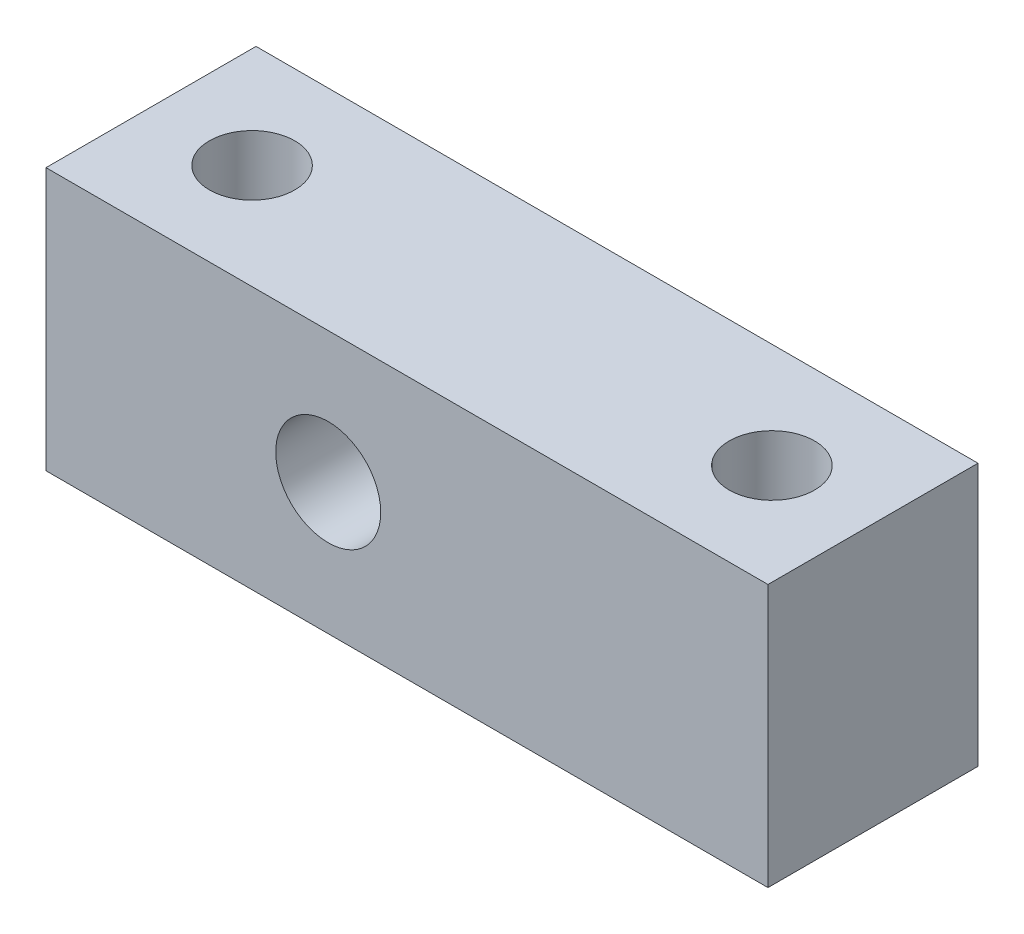
SolidWorks part; units mm, degrees
ref_plane "Спереди" through (0, 0, 0) normal (0, 0, 1) x (1, 0, 0)
ref_plane "Сверху" through (0, 0, 0) normal (0, 1, 0) x (1, 0, 0)
ref_plane "Справа" through (0, 0, 0) normal (1, 0, 0) x (0, 0, -1)
sketch "Эскиз1" plane through (0, 0, 0) normal (0, 0, 1) x (1, 0, 0)
  line L1 (-27.5, -10) -> (27.5, -10)
  line L2 (-27.5, -10) -> (-27.5, 10)
  line L3 (-27.5, 10) -> (27.5, 10)
  line L4 (27.5, -10) -> (27.5, 10)
  line L5 (-27.5, -10) -> (27.5, 10) construction
  line L6 (-27.5, 10) -> (27.5, -10) construction
  point P0 (0, 0)
  dimension "D1" = 55
  dimension "D2" = 20
extrude "Бобышка-Вытянуть1" add sketch "Эскиз1" along normal blind 16
sketch "Эскиз2" plane through (0, 0, 16) normal (0, 0, 1) x (1, 0, 0)
  circle A0 centre (-6, 0) radius 4
  dimension "D1" = 8
  dimension "D2" = 6
extrude "Вырез-Вытянуть1" cut sketch "Эскиз2" against normal blind 18
hole_wizard "Диаметр отверстия Ø6.5 (6.5)1" positions "Эскиз3" profile "Эскиз4" hole size "Ø6.5" standard "DIN" end condition through all
sketch "Эскиз3" plane through (0, 10, 0) normal (0, 1, 0) x (1, 0, 0)
  line L0 (27.5, 0) -> (-27.5, 0) construction
  point P0 (19.8, -8)
  point P2 (-19.8, -8)
  dimension "D1" = 8
  dimension "D2" = 19.8
  dimension "D3" = 39.6
sketch "Эскиз4" plane through (19.8, 10, 8) normal (1, 0, 0) x (0, 0, 1)
  line L0 (0, 0) -> (0, 20)
  line L1 (0, 20) -> (3.25, 20)
  line L2 (3.25, 20) -> (3.25, 0)
  line L5 (3.25, 0) -> (0, 0)
  line L11 (0, -6.35) -> (0, 107.95) construction
  dimension "Диаметр сквозного отверстия" = 6.5
  dimension "Глубина сквозного отверстия" = 20
